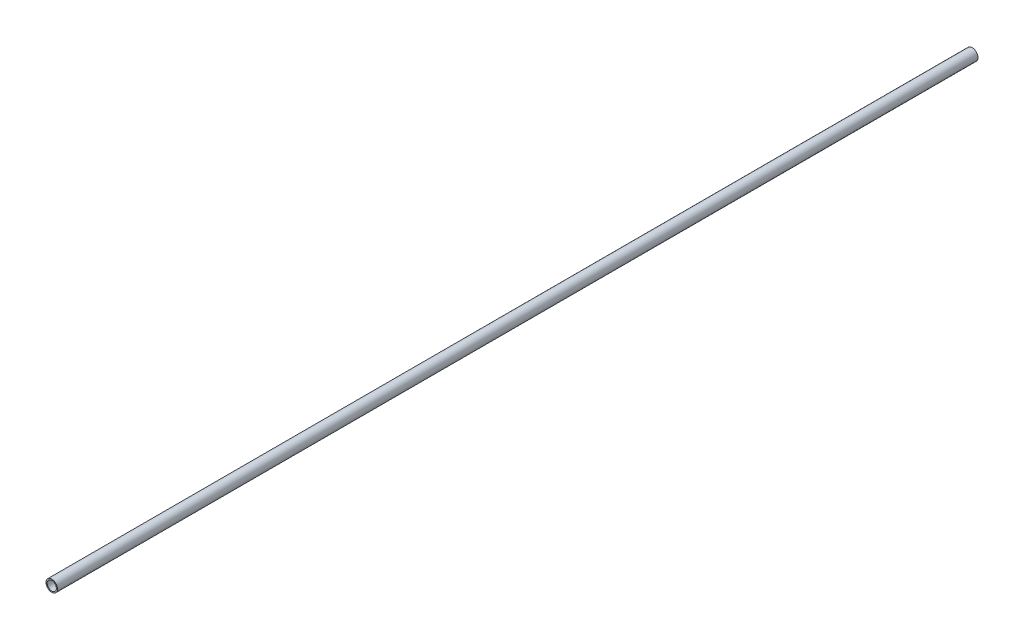
SolidWorks part; units mm, degrees
ref_plane "Front Plane" through (0, 0, 0) normal (0, 0, 1) x (1, 0, 0)
ref_plane "Top Plane" through (0, 0, 0) normal (0, 1, 0) x (1, 0, 0)
ref_plane "Right Plane" through (0, 0, 0) normal (1, 0, 0) x (0, 0, -1)
sketch "Sketch1" plane through (0, 0, 0) normal (0, 0, 1) x (1, 0, 0)
  circle A0 centre (0, 0) radius 5
  circle A1 centre (0, 0) radius 4
  dimension "D1" = 10
  dimension "D2" = 8
extrude "Boss-Extrude1" add sketch "Sketch1" along normal blind 800
